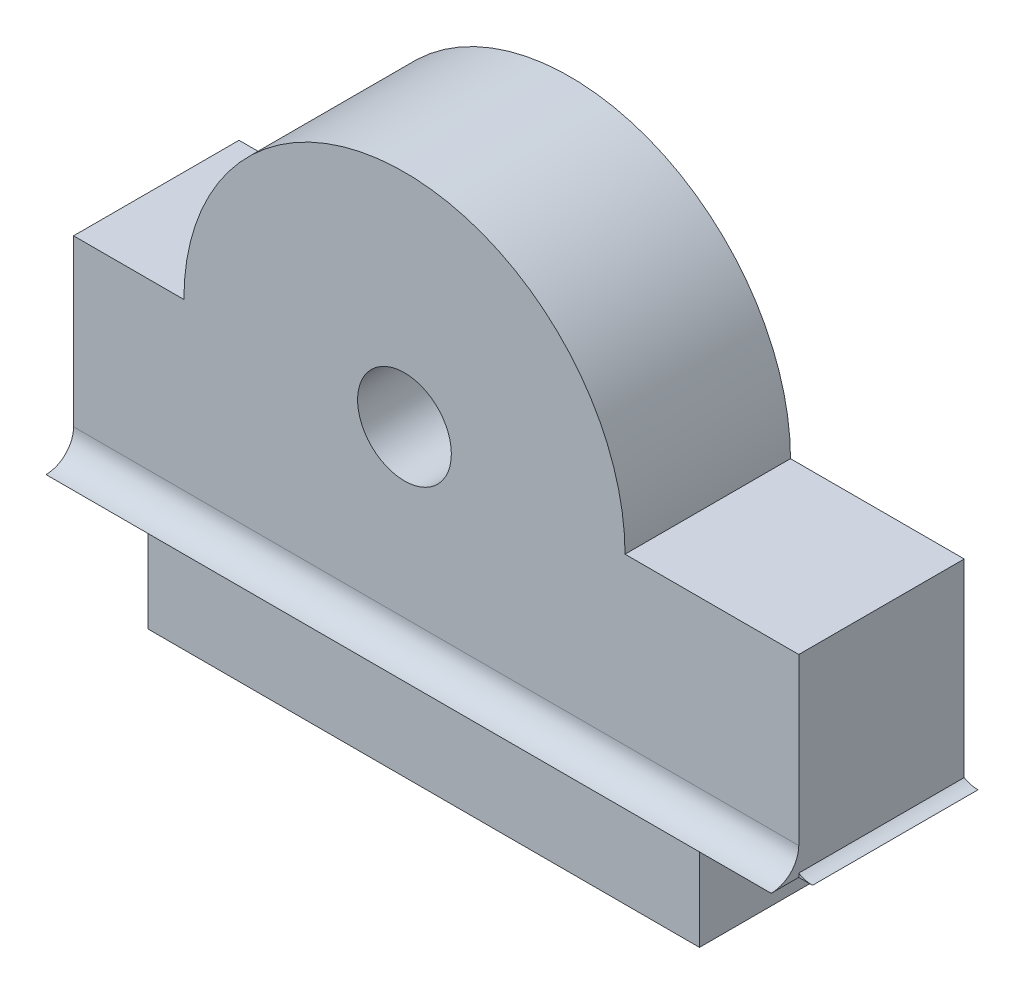
SolidWorks part; units mm, degrees
ref_plane "Front Plane" through (0, 0, 0) normal (0, 0, 1) x (1, 0, 0)
ref_plane "Top Plane" through (0, 0, 0) normal (0, 1, 0) x (1, 0, 0)
ref_plane "Right Plane" through (0, 0, 0) normal (1, 0, 0) x (0, 0, -1)
sketch "Sketch1" plane through (0, 0, 0) normal (0, 0, 1) x (1, 0, 0)
  line L0 (0, 0) -> (20, 0)
  line L1 (0, 0) -> (0, 4)
  line L2 (20, 0) -> (20, 4)
  line L3 (0, 4) -> (-2.7, 4)
  line L4 (23.6, 11) -> (23.6, 4)
  line L5 (-2.7, 4) -> (-2.7, 11)
  line L6 (-2.7, 11) -> (1.3, 11)
  line L7 (17.3, 11) -> (23.6, 11)
  line L8 (23.6, 4) -> (20, 4)
  line L11 (11.1187, 14.15) -> (7.4813, 14.15)
  line L12 (7.4813, 14.15) -> (5.6627, 11)
  line L13 (5.6627, 11) -> (7.4813, 7.85)
  line L14 (7.4813, 7.85) -> (11.1187, 7.85)
  line L15 (11.1187, 7.85) -> (12.9373, 11)
  line L16 (12.9373, 11) -> (11.1187, 14.15)
  arc A0 (17.3, 11) -> (1.3, 11) centre (9.3, 11) ccw
  circle A1 centre (9.3, 10.95) radius 3.2 construction
  point P19 (10, 0)
  dimension "D5" = 23.6
  dimension "D6" = 20
  dimension "D2" = 7
  dimension "D4" = 6.4
  dimension "D7" = 2.7
  dimension "D9" = 4
extrude "Boss-Extrude1" add sketch "Sketch1" along normal blind 6
sketch "Sketch2" plane through (-2.7, 0, 0) normal (-1, 0, 0) x (0, 0, 1)
  line L0 (3, 0) -> (3, 7) construction
  line L1 (6, 4) -> (6, 5)
  line L2 (6, 4) -> (7, 4)
  line L3 (0, 4) -> (-1, 4) construction
  line L4 (0, 4) -> (0, 5) construction
  arc A0 (6, 5) -> (7, 4) centre (7, 5) ccw
  arc A1 (0, 5) -> (-1, 4) centre (-1, 5) cw construction
  dimension "D1" = 1
  dimension "D2" = 1
  dimension "D3" = 6
  dimension "D4" = 3
  dimension "D5" = 4
extrude "Boss-Extrude2" add sketch "Sketch2" against normal up to surface (26.3 mm away) up to face at (23.6, 7.5, 3)
sketch "Sketch4" plane through (0, 0, 6) normal (0, 0, 1) x (1, 0, 0)
  line L0 (10.8, 0) -> (10.8, 7) construction
  line L1 (23.1, 4) -> (23.1, 5)
  line L2 (23.1, 4) -> (24.1, 4)
  line L3 (-1.5, 4) -> (-2.5, 4)
  line L4 (-1.5, 4) -> (-1.5, 5)
  arc A0 (23.1, 5) -> (24.1, 4) centre (24.1, 5) ccw
  arc A1 (-1.5, 5) -> (-2.5, 4) centre (-2.5, 5) cw
  dimension "D1" = 1
  dimension "D2" = 1
  dimension "D3" = 10.8
  dimension "D4" = 12.3
  dimension "D5" = 4
extrude "Boss-Extrude3" add sketch "Sketch4" against normal up to surface (6 mm away) up to face at (10.04, 6.8, 0)
sketch "Sketch8" plane through (0, 0, 6) normal (0, 0, 1) x (1, 0, 0)
  line L0 (5.6627, 11) -> (12.9373, 11) construction
  line L1 (11.1187, 14.15) -> (7.4813, 14.15) construction
  line L4 (7.4525, 14.2) -> (5.605, 11)
  line L5 (5.605, 11) -> (7.4525, 7.8)
  line L6 (7.4525, 7.8) -> (11.1475, 7.8)
  line L7 (11.1475, 7.8) -> (12.995, 11)
  line L8 (12.995, 11) -> (11.1475, 14.2)
  line L9 (11.1475, 14.2) -> (7.4525, 14.2)
  circle A0 centre (9.3, 11) radius 3.2 construction
  circle A1 centre (9.3, 11) radius 1.7
  point P4 (9.3, 11)
  point P6 (9.3, 7.8)
  point P14 (9.3, 14.15)
  dimension "D1" = 6.4
  dimension "D2" = 3.4
extrude "Boss-Extrude4" add sketch "Sketch8" against normal blind 3
equation "\"D4@Sketch1\" = 6 + \"tol1@parametersSketch@prostheticParameters.SLDPRT\""
equation "\"D1@Sketch8\"= 6 + \"tol1@parametersSketch@prostheticParameters.SLDPRT\""
equation "\"D2@Sketch8\"= 3 + \"tol1@parametersSketch@prostheticParameters.SLDPRT\""
